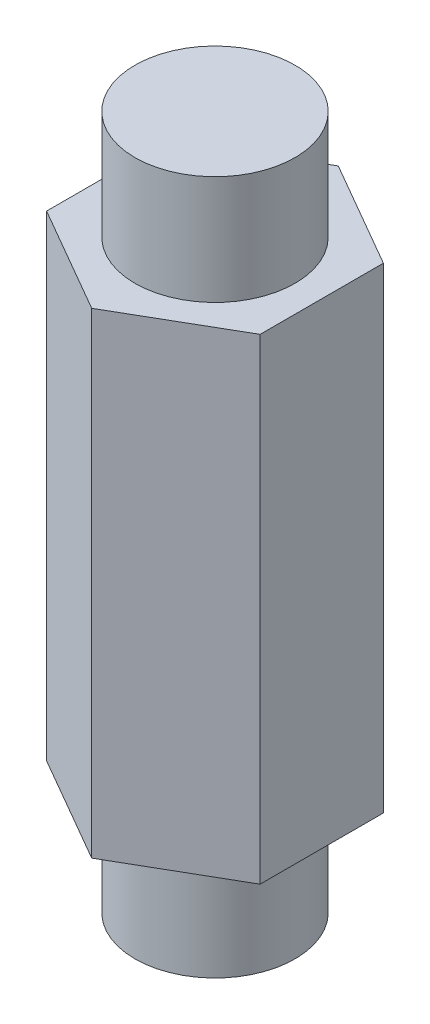
SolidWorks part; units mm, degrees
material "7075-T6 (SN)"
ref_plane "Front Plane" through (0, 0, 0) normal (0, 0, 1) x (1, 0, 0)
ref_plane "Top Plane" through (0, 0, 0) normal (0, 1, 0) x (1, 0, 0)
ref_plane "Right Plane" through (0, 0, 0) normal (1, 0, 0) x (0, 0, -1)
sketch "Sketch1" plane through (0, 0, 0) normal (0, 1, 0) x (1, 0, 0)
  line L1 (6.35, -3.6662) -> (6.35, 3.6662)
  line L2 (6.35, 3.6662) -> (0, 7.3323)
  line L3 (0, 7.3323) -> (-6.35, 3.6662)
  line L4 (-6.35, 3.6662) -> (-6.35, -3.6662)
  line L5 (-6.35, -3.6662) -> (0, -7.3323)
  line L6 (0, -7.3323) -> (6.35, -3.6662)
  circle A0 centre (0, 0) radius 6.35 construction
  dimension "D1" = 12.7
extrude "Boss-Extrude1" add sketch "Sketch1" along normal mid plane 28.321
sketch "Sketch2" plane through (0, 0, 0) normal (0, 1, 0) x (1, 0, 0)
  circle A0 centre (0, 0) radius 4.7625
  dimension "D1" = 9.525
extrude "Boss-Extrude2" add sketch "Sketch2" along normal mid plane 41.275
